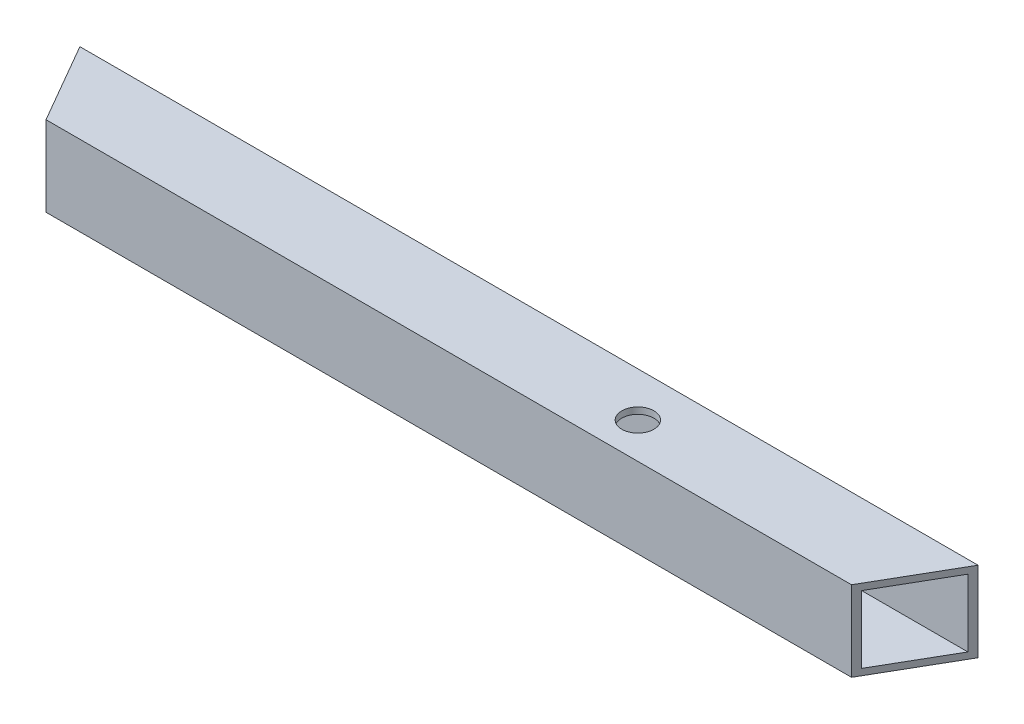
SolidWorks part; units mm, degrees
ref_plane "Front Plane" through (0, 0, 0) normal (0, 0, 1) x (1, 0, 0)
ref_plane "Top Plane" through (0, 0, 0) normal (0, 1, 0) x (1, 0, 0)
ref_plane "Right Plane" through (0, 0, 0) normal (1, 0, 0) x (0, 0, -1)
sketch "Sketch1" plane through (0, 0, 0) normal (0, 1, 0) x (1, 0, 0)
  line L0 (125.5662, 217.4871) -> (-125.5662, 217.4871)
  line L2 (140, 242.4871) -> (-140, 242.4871)
  line L12 (-140, 242.4871) -> (-125.5662, 217.4871)
  line L13 (125.5662, 217.4871) -> (140, 242.4871)
  line L14 (280, 0) -> (140, 242.4871) construction
  line L16 (251.1325, 0) -> (125.5662, 217.4871) construction
  line L18 (-125.5662, 217.4871) -> (-251.1325, 0) construction
  line L19 (-140, 242.4871) -> (-280, 0) construction
  line L22 (-251.1325, 0) -> (-125.5662, -217.4871) construction
  line L23 (-280, 0) -> (-140, -242.4871) construction
  line L26 (-125.5662, -217.4871) -> (125.5662, -217.4871) construction
  line L27 (-140, -242.4871) -> (140, -242.4871) construction
  line L30 (125.5662, -217.4871) -> (251.1325, 0) construction
  line L31 (140, -242.4871) -> (280, 0) construction
  dimension "D1" = 280
  dimension "D2" = 25
extrude "Boss-Extrude1" add sketch "Sketch1" along normal blind 25
shell "Shell1" thickness 2
sketch "Sketch2" plane through (0, 25, 0) normal (0, 1, 0) x (1, 0, 0)
  line L0 (47.7831, 228.6574) -> (132.7831, 229.9871) construction
  line L1 (125.5662, 217.4871) -> (140, 242.4871) construction
  circle A0 centre (47.7831, 228.6574) radius 5
  dimension "D1" = 85
extrude "Cut-Extrude1" cut sketch "Sketch2" against normal blind 53
